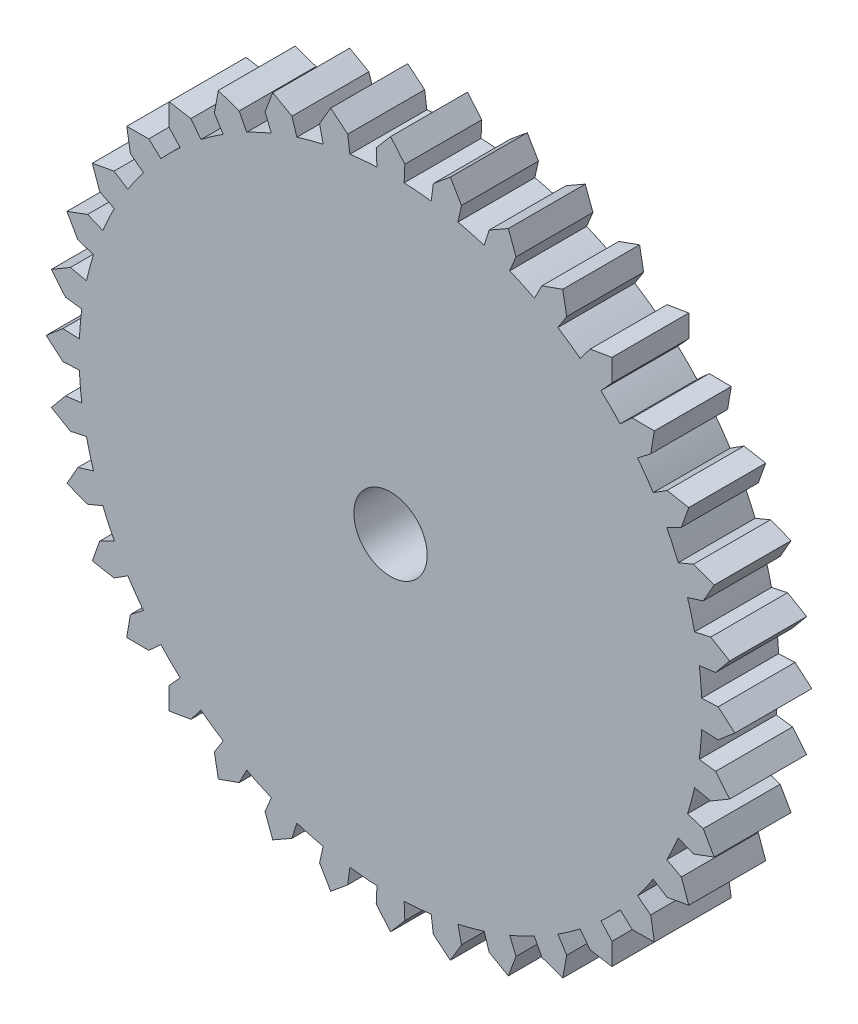
SolidWorks part; units mm, degrees
ref_plane "Front Plane" through (0, 0, 0) normal (0, 0, 1) x (1, 0, 0)
ref_plane "Top Plane" through (0, 0, 0) normal (0, 1, 0) x (1, 0, 0)
ref_plane "Right Plane" through (0, 0, 0) normal (1, 0, 0) x (0, 0, -1)
sketch "Sketch1" plane through (0, 0, 0) normal (0, 0, 1) x (1, 0, 0)
  line L0 (1.6323, 9.2572) -> (1.9371, 8.7378)
  line L1 (0, 9.4) -> (0.3904, 8.9415)
  line L2 (-0.3708, 8.4919) -> (-0.3904, 8.9415)
  line L3 (0, 9.4) -> (-0.3904, 8.9415)
  line L4 (0.3708, 8.4919) -> (0.3904, 8.9415)
  line L5 (1.1095, 8.4273) -> (1.1682, 8.8734)
  line L6 (1.6323, 9.2572) -> (1.1682, 8.8734)
  line L7 (1.8397, 8.2985) -> (1.9371, 8.7378)
  line L8 (3.215, 8.8331) -> (3.425, 8.2687)
  line L9 (2.556, 8.1066) -> (2.6913, 8.5358)
  line L10 (3.215, 8.8331) -> (2.6913, 8.5358)
  line L11 (3.2528, 7.853) -> (3.425, 8.2687)
  line L12 (4.7, 8.1406) -> (4.8088, 7.5484)
  line L13 (3.9249, 7.5396) -> (4.1327, 7.9387)
  line L14 (4.7, 8.1406) -> (4.1327, 7.9387)
  line L15 (4.567, 7.1688) -> (4.8088, 7.5484)
  line L16 (6.0422, 7.2008) -> (6.0465, 6.5986)
  line L17 (5.1745, 6.7435) -> (5.4484, 7.1005)
  line L18 (6.0422, 7.2008) -> (5.4484, 7.1005)
  line L19 (5.7425, 6.2669) -> (6.0465, 6.5986)
  line L20 (7.2008, 6.0422) -> (7.1005, 5.4484)
  line L21 (6.2669, 5.7425) -> (6.5986, 6.0465)
  line L22 (7.2008, 6.0422) -> (6.5986, 6.0465)
  line L23 (6.7435, 5.1745) -> (7.1005, 5.4484)
  line L24 (8.1406, 4.7) -> (7.9387, 4.1327)
  line L25 (7.1688, 4.567) -> (7.5484, 4.8088)
  line L26 (8.1406, 4.7) -> (7.5484, 4.8088)
  line L27 (7.5396, 3.9249) -> (7.9387, 4.1327)
  line L28 (8.8331, 3.215) -> (8.5358, 2.6913)
  line L29 (7.853, 3.2528) -> (8.2687, 3.425)
  line L30 (8.8331, 3.215) -> (8.2687, 3.425)
  line L31 (8.1066, 2.556) -> (8.5358, 2.6913)
  line L32 (9.2572, 1.6323) -> (8.8734, 1.1682)
  line L33 (8.2985, 1.8397) -> (8.7378, 1.9371)
  line L34 (9.2572, 1.6323) -> (8.7378, 1.9371)
  line L35 (8.4273, 1.1095) -> (8.8734, 1.1682)
  line L36 (9.4, 0) -> (8.9415, -0.3904)
  line L37 (8.4919, 0.3708) -> (8.9415, 0.3904)
  line L38 (9.4, 0) -> (8.9415, 0.3904)
  line L39 (8.4919, -0.3708) -> (8.9415, -0.3904)
  line L40 (9.2572, -1.6323) -> (8.7378, -1.9371)
  line L41 (8.4273, -1.1095) -> (8.8734, -1.1682)
  line L42 (9.2572, -1.6323) -> (8.8734, -1.1682)
  line L43 (8.2985, -1.8397) -> (8.7378, -1.9371)
  line L44 (8.8331, -3.215) -> (8.2687, -3.425)
  line L45 (8.1066, -2.556) -> (8.5358, -2.6913)
  line L46 (8.8331, -3.215) -> (8.5358, -2.6913)
  line L47 (7.853, -3.2528) -> (8.2687, -3.425)
  line L48 (8.1406, -4.7) -> (7.5484, -4.8088)
  line L49 (7.5396, -3.9249) -> (7.9387, -4.1327)
  line L50 (8.1406, -4.7) -> (7.9387, -4.1327)
  line L51 (7.1688, -4.567) -> (7.5484, -4.8088)
  line L52 (7.2008, -6.0422) -> (6.5986, -6.0465)
  line L53 (6.7435, -5.1745) -> (7.1005, -5.4484)
  line L54 (7.2008, -6.0422) -> (7.1005, -5.4484)
  line L55 (6.2669, -5.7425) -> (6.5986, -6.0465)
  line L56 (6.0422, -7.2008) -> (5.4484, -7.1005)
  line L57 (5.7425, -6.2669) -> (6.0465, -6.5986)
  line L58 (6.0422, -7.2008) -> (6.0465, -6.5986)
  line L59 (5.1745, -6.7435) -> (5.4484, -7.1005)
  line L60 (4.7, -8.1406) -> (4.1327, -7.9387)
  line L61 (4.567, -7.1688) -> (4.8088, -7.5484)
  line L62 (4.7, -8.1406) -> (4.8088, -7.5484)
  line L63 (3.9249, -7.5396) -> (4.1327, -7.9387)
  line L64 (3.215, -8.8331) -> (2.6913, -8.5358)
  line L65 (3.2528, -7.853) -> (3.425, -8.2687)
  line L66 (3.215, -8.8331) -> (3.425, -8.2687)
  line L67 (2.556, -8.1066) -> (2.6913, -8.5358)
  line L68 (1.6323, -9.2572) -> (1.1682, -8.8734)
  line L69 (1.8397, -8.2985) -> (1.9371, -8.7378)
  line L70 (1.6323, -9.2572) -> (1.9371, -8.7378)
  line L71 (1.1095, -8.4273) -> (1.1682, -8.8734)
  line L72 (0, -9.4) -> (-0.3904, -8.9415)
  line L73 (0.3708, -8.4919) -> (0.3904, -8.9415)
  line L74 (0, -9.4) -> (0.3904, -8.9415)
  line L75 (-0.3708, -8.4919) -> (-0.3904, -8.9415)
  line L76 (-1.6323, -9.2572) -> (-1.9371, -8.7378)
  line L77 (-1.1095, -8.4273) -> (-1.1682, -8.8734)
  line L78 (-1.6323, -9.2572) -> (-1.1682, -8.8734)
  line L79 (-1.8397, -8.2985) -> (-1.9371, -8.7378)
  line L80 (-3.215, -8.8331) -> (-3.425, -8.2687)
  line L81 (-2.556, -8.1066) -> (-2.6913, -8.5358)
  line L82 (-3.215, -8.8331) -> (-2.6913, -8.5358)
  line L83 (-3.2528, -7.853) -> (-3.425, -8.2687)
  line L84 (-4.7, -8.1406) -> (-4.8088, -7.5484)
  line L85 (-3.9249, -7.5396) -> (-4.1327, -7.9387)
  line L86 (-4.7, -8.1406) -> (-4.1327, -7.9387)
  line L87 (-4.567, -7.1688) -> (-4.8088, -7.5484)
  line L88 (-6.0422, -7.2008) -> (-6.0465, -6.5986)
  line L89 (-5.1745, -6.7435) -> (-5.4484, -7.1005)
  line L90 (-6.0422, -7.2008) -> (-5.4484, -7.1005)
  line L91 (-5.7425, -6.2669) -> (-6.0465, -6.5986)
  line L92 (-7.2008, -6.0422) -> (-7.1005, -5.4484)
  line L93 (-6.2669, -5.7425) -> (-6.5986, -6.0465)
  line L94 (-7.2008, -6.0422) -> (-6.5986, -6.0465)
  line L95 (-6.7435, -5.1745) -> (-7.1005, -5.4484)
  line L96 (-8.1406, -4.7) -> (-7.9387, -4.1327)
  line L97 (-7.1688, -4.567) -> (-7.5484, -4.8088)
  line L98 (-8.1406, -4.7) -> (-7.5484, -4.8088)
  line L99 (-7.5396, -3.9249) -> (-7.9387, -4.1327)
  line L100 (-8.8331, -3.215) -> (-8.5358, -2.6913)
  line L101 (-7.853, -3.2528) -> (-8.2687, -3.425)
  line L102 (-8.8331, -3.215) -> (-8.2687, -3.425)
  line L103 (-8.1066, -2.556) -> (-8.5358, -2.6913)
  line L104 (-9.2572, -1.6323) -> (-8.8734, -1.1682)
  line L105 (-8.2985, -1.8397) -> (-8.7378, -1.9371)
  line L106 (-9.2572, -1.6323) -> (-8.7378, -1.9371)
  line L107 (-8.4273, -1.1095) -> (-8.8734, -1.1682)
  line L108 (-9.4, 0) -> (-8.9415, 0.3904)
  line L109 (-8.4919, -0.3708) -> (-8.9415, -0.3904)
  line L110 (-9.4, 0) -> (-8.9415, -0.3904)
  line L111 (-8.4919, 0.3708) -> (-8.9415, 0.3904)
  line L112 (-9.2572, 1.6323) -> (-8.7378, 1.9371)
  line L113 (-8.4273, 1.1095) -> (-8.8734, 1.1682)
  line L114 (-9.2572, 1.6323) -> (-8.8734, 1.1682)
  line L115 (-8.2985, 1.8397) -> (-8.7378, 1.9371)
  line L116 (-8.8331, 3.215) -> (-8.2687, 3.425)
  line L117 (-8.1066, 2.556) -> (-8.5358, 2.6913)
  line L118 (-8.8331, 3.215) -> (-8.5358, 2.6913)
  line L119 (-7.853, 3.2528) -> (-8.2687, 3.425)
  line L120 (-8.1406, 4.7) -> (-7.5484, 4.8088)
  line L121 (-7.5396, 3.9249) -> (-7.9387, 4.1327)
  line L122 (-8.1406, 4.7) -> (-7.9387, 4.1327)
  line L123 (-7.1688, 4.567) -> (-7.5484, 4.8088)
  line L124 (-7.2008, 6.0422) -> (-6.5986, 6.0465)
  line L125 (-6.7435, 5.1745) -> (-7.1005, 5.4484)
  line L126 (-7.2008, 6.0422) -> (-7.1005, 5.4484)
  line L127 (-6.2669, 5.7425) -> (-6.5986, 6.0465)
  line L128 (-6.0422, 7.2008) -> (-5.4484, 7.1005)
  line L129 (-5.7425, 6.2669) -> (-6.0465, 6.5986)
  line L130 (-6.0422, 7.2008) -> (-6.0465, 6.5986)
  line L131 (-5.1745, 6.7435) -> (-5.4484, 7.1005)
  line L132 (-4.7, 8.1406) -> (-4.1327, 7.9387)
  line L133 (-4.567, 7.1688) -> (-4.8088, 7.5484)
  line L134 (-4.7, 8.1406) -> (-4.8088, 7.5484)
  line L135 (-3.9249, 7.5396) -> (-4.1327, 7.9387)
  line L136 (-3.215, 8.8331) -> (-2.6913, 8.5358)
  line L137 (-3.2528, 7.853) -> (-3.425, 8.2687)
  line L138 (-3.215, 8.8331) -> (-3.425, 8.2687)
  line L139 (-2.556, 8.1066) -> (-2.6913, 8.5358)
  line L140 (-1.6323, 9.2572) -> (-1.1682, 8.8734)
  line L141 (-1.8397, 8.2985) -> (-1.9371, 8.7378)
  line L142 (-1.6323, 9.2572) -> (-1.9371, 8.7378)
  line L143 (-1.1095, 8.4273) -> (-1.1682, 8.8734)
  arc A0 (0.3708, 8.4919) -> (0.7408, 8.4677) centre (0, 0) cw
  arc A1 (-0.3708, 8.4919) -> (-0.7408, 8.4677) centre (0, 0) ccw
  arc A2 (1.8397, 8.2985) -> (2.2, 8.2104) centre (0, 0) cw
  arc A3 (1.1095, 8.4273) -> (0.7408, 8.4677) centre (0, 0) ccw
  arc A4 (3.2528, 7.853) -> (3.5923, 7.7036) centre (0, 0) cw
  arc A5 (2.556, 8.1066) -> (2.2, 8.2104) centre (0, 0) ccw
  arc A6 (4.567, 7.1688) -> (4.8754, 6.9628) centre (0, 0) cw
  arc A7 (3.9249, 7.5396) -> (3.5923, 7.7036) centre (0, 0) ccw
  arc A8 (5.7425, 6.2669) -> (6.0104, 6.0104) centre (0, 0) cw
  arc A9 (5.1745, 6.7435) -> (4.8754, 6.9628) centre (0, 0) ccw
  arc A10 (6.7435, 5.1745) -> (6.9628, 4.8754) centre (0, 0) cw
  arc A11 (6.2669, 5.7425) -> (6.0104, 6.0104) centre (0, 0) ccw
  arc A12 (7.5396, 3.9249) -> (7.7036, 3.5923) centre (0, 0) cw
  arc A13 (7.1688, 4.567) -> (6.9628, 4.8754) centre (0, 0) ccw
  arc A14 (8.1066, 2.556) -> (8.2104, 2.2) centre (0, 0) cw
  arc A15 (7.853, 3.2528) -> (7.7036, 3.5923) centre (0, 0) ccw
  arc A16 (8.4273, 1.1095) -> (8.4677, 0.7408) centre (0, 0) cw
  arc A17 (8.2985, 1.8397) -> (8.2104, 2.2) centre (0, 0) ccw
  arc A18 (8.4919, -0.3708) -> (8.4677, -0.7408) centre (0, 0) cw
  arc A19 (8.4919, 0.3708) -> (8.4677, 0.7408) centre (0, 0) ccw
  arc A20 (8.2985, -1.8397) -> (8.2104, -2.2) centre (0, 0) cw
  arc A21 (8.4273, -1.1095) -> (8.4677, -0.7408) centre (0, 0) ccw
  arc A22 (7.853, -3.2528) -> (7.7036, -3.5923) centre (0, 0) cw
  arc A23 (8.1066, -2.556) -> (8.2104, -2.2) centre (0, 0) ccw
  arc A24 (7.1688, -4.567) -> (6.9628, -4.8754) centre (0, 0) cw
  arc A25 (7.5396, -3.9249) -> (7.7036, -3.5923) centre (0, 0) ccw
  arc A26 (6.2669, -5.7425) -> (6.0104, -6.0104) centre (0, 0) cw
  arc A27 (6.7435, -5.1745) -> (6.9628, -4.8754) centre (0, 0) ccw
  arc A28 (5.1745, -6.7435) -> (4.8754, -6.9628) centre (0, 0) cw
  arc A29 (5.7425, -6.2669) -> (6.0104, -6.0104) centre (0, 0) ccw
  arc A30 (3.9249, -7.5396) -> (3.5923, -7.7036) centre (0, 0) cw
  arc A31 (4.567, -7.1688) -> (4.8754, -6.9628) centre (0, 0) ccw
  arc A32 (2.556, -8.1066) -> (2.2, -8.2104) centre (0, 0) cw
  arc A33 (3.2528, -7.853) -> (3.5923, -7.7036) centre (0, 0) ccw
  arc A34 (1.1095, -8.4273) -> (0.7408, -8.4677) centre (0, 0) cw
  arc A35 (1.8397, -8.2985) -> (2.2, -8.2104) centre (0, 0) ccw
  arc A36 (-0.3708, -8.4919) -> (-0.7408, -8.4677) centre (0, 0) cw
  arc A37 (0.3708, -8.4919) -> (0.7408, -8.4677) centre (0, 0) ccw
  arc A38 (-1.8397, -8.2985) -> (-2.2, -8.2104) centre (0, 0) cw
  arc A39 (-1.1095, -8.4273) -> (-0.7408, -8.4677) centre (0, 0) ccw
  arc A40 (-3.2528, -7.853) -> (-3.5923, -7.7036) centre (0, 0) cw
  arc A41 (-2.556, -8.1066) -> (-2.2, -8.2104) centre (0, 0) ccw
  arc A42 (-4.567, -7.1688) -> (-4.8754, -6.9628) centre (0, 0) cw
  arc A43 (-3.9249, -7.5396) -> (-3.5923, -7.7036) centre (0, 0) ccw
  arc A44 (-5.7425, -6.2669) -> (-6.0104, -6.0104) centre (0, 0) cw
  arc A45 (-5.1745, -6.7435) -> (-4.8754, -6.9628) centre (0, 0) ccw
  arc A46 (-6.7435, -5.1745) -> (-6.9628, -4.8754) centre (0, 0) cw
  arc A47 (-6.2669, -5.7425) -> (-6.0104, -6.0104) centre (0, 0) ccw
  arc A48 (-7.5396, -3.9249) -> (-7.7036, -3.5923) centre (0, 0) cw
  arc A49 (-7.1688, -4.567) -> (-6.9628, -4.8754) centre (0, 0) ccw
  arc A50 (-8.1066, -2.556) -> (-8.2104, -2.2) centre (0, 0) cw
  arc A51 (-7.853, -3.2528) -> (-7.7036, -3.5923) centre (0, 0) ccw
  arc A52 (-8.4273, -1.1095) -> (-8.4677, -0.7408) centre (0, 0) cw
  arc A53 (-8.2985, -1.8397) -> (-8.2104, -2.2) centre (0, 0) ccw
  arc A54 (-8.4919, 0.3708) -> (-8.4677, 0.7408) centre (0, 0) cw
  arc A55 (-8.4919, -0.3708) -> (-8.4677, -0.7408) centre (0, 0) ccw
  arc A56 (-8.2985, 1.8397) -> (-8.2104, 2.2) centre (0, 0) cw
  arc A57 (-8.4273, 1.1095) -> (-8.4677, 0.7408) centre (0, 0) ccw
  arc A58 (-7.853, 3.2528) -> (-7.7036, 3.5923) centre (0, 0) cw
  arc A59 (-8.1066, 2.556) -> (-8.2104, 2.2) centre (0, 0) ccw
  arc A60 (-7.1688, 4.567) -> (-6.9628, 4.8754) centre (0, 0) cw
  arc A61 (-7.5396, 3.9249) -> (-7.7036, 3.5923) centre (0, 0) ccw
  arc A62 (-6.2669, 5.7425) -> (-6.0104, 6.0104) centre (0, 0) cw
  arc A63 (-6.7435, 5.1745) -> (-6.9628, 4.8754) centre (0, 0) ccw
  arc A64 (-5.1745, 6.7435) -> (-4.8754, 6.9628) centre (0, 0) cw
  arc A65 (-5.7425, 6.2669) -> (-6.0104, 6.0104) centre (0, 0) ccw
  arc A66 (-3.9249, 7.5396) -> (-3.5923, 7.7036) centre (0, 0) cw
  arc A67 (-4.567, 7.1688) -> (-4.8754, 6.9628) centre (0, 0) ccw
  arc A68 (-2.556, 8.1066) -> (-2.2, 8.2104) centre (0, 0) cw
  arc A69 (-3.2528, 7.853) -> (-3.5923, 7.7036) centre (0, 0) ccw
  arc A70 (-1.1095, 8.4273) -> (-0.7408, 8.4677) centre (0, 0) cw
  arc A71 (-1.8397, 8.2985) -> (-2.2, 8.2104) centre (0, 0) ccw
  circle A72 centre (0, 0) radius 1
  point P256 (0, 0)
  dimension "D1" = 36
  dimension "D2" = 17
  dimension "D3" = 2
extrude "Boss-Extrude1" add sketch "Sketch1" along normal blind 2.1
sketch "Sketch2" plane through (0, 0, 0) normal (0, 0, 1) x (1, 0, 0)
  line L0 (1.85, 3.2043) -> (1.8872, 2.4594)
  line L1 (0, 3.7) -> (0.4046, 3.0735)
  line L2 (-0.3263, 2.4786) -> (-0.4046, 3.0735)
  line L3 (0, 3.7) -> (-0.4046, 3.0735)
  line L4 (0.3263, 2.4786) -> (0.4046, 3.0735)
  line L5 (0.9567, 2.3097) -> (1.1863, 2.864)
  line L6 (1.85, 3.2043) -> (1.1863, 2.864)
  line L7 (1.5219, 1.9834) -> (1.8872, 2.4594)
  line L8 (3.2043, 1.85) -> (2.864, 1.1863)
  line L9 (1.9834, 1.5219) -> (2.4594, 1.8872)
  line L10 (3.2043, 1.85) -> (2.4594, 1.8872)
  line L11 (2.3097, 0.9567) -> (2.864, 1.1863)
  line L12 (3.7, 0) -> (3.0735, -0.4046)
  line L13 (2.4786, 0.3263) -> (3.0735, 0.4046)
  line L14 (3.7, 0) -> (3.0735, 0.4046)
  line L15 (2.4786, -0.3263) -> (3.0735, -0.4046)
  line L16 (3.2043, -1.85) -> (2.4594, -1.8872)
  line L17 (2.3097, -0.9567) -> (2.864, -1.1863)
  line L18 (3.2043, -1.85) -> (2.864, -1.1863)
  line L19 (1.9834, -1.5219) -> (2.4594, -1.8872)
  line L20 (1.85, -3.2043) -> (1.1863, -2.864)
  line L21 (1.5219, -1.9834) -> (1.8872, -2.4594)
  line L22 (1.85, -3.2043) -> (1.8872, -2.4594)
  line L23 (0.9567, -2.3097) -> (1.1863, -2.864)
  line L24 (0, -3.7) -> (-0.4046, -3.0735)
  line L25 (0.3263, -2.4786) -> (0.4046, -3.0735)
  line L26 (0, -3.7) -> (0.4046, -3.0735)
  line L27 (-0.3263, -2.4786) -> (-0.4046, -3.0735)
  line L28 (-1.85, -3.2043) -> (-1.8872, -2.4594)
  line L29 (-0.9567, -2.3097) -> (-1.1863, -2.864)
  line L30 (-1.85, -3.2043) -> (-1.1863, -2.864)
  line L31 (-1.5219, -1.9834) -> (-1.8872, -2.4594)
  line L32 (-3.2043, -1.85) -> (-2.864, -1.1863)
  line L33 (-1.9834, -1.5219) -> (-2.4594, -1.8872)
  line L34 (-3.2043, -1.85) -> (-2.4594, -1.8872)
  line L35 (-2.3097, -0.9567) -> (-2.864, -1.1863)
  line L36 (-3.7, 0) -> (-3.0735, 0.4046)
  line L37 (-2.4786, -0.3263) -> (-3.0735, -0.4046)
  line L38 (-3.7, 0) -> (-3.0735, -0.4046)
  line L39 (-2.4786, 0.3263) -> (-3.0735, 0.4046)
  line L40 (-3.2043, 1.85) -> (-2.4594, 1.8872)
  line L41 (-2.3097, 0.9567) -> (-2.864, 1.1863)
  line L42 (-3.2043, 1.85) -> (-2.864, 1.1863)
  line L43 (-1.9834, 1.5219) -> (-2.4594, 1.8872)
  line L44 (-1.85, 3.2043) -> (-1.1863, 2.864)
  line L45 (-1.5219, 1.9834) -> (-1.8872, 2.4594)
  line L46 (-1.85, 3.2043) -> (-1.8872, 2.4594)
  line L47 (-0.9567, 2.3097) -> (-1.1863, 2.864)
  arc A0 (0.3263, 2.4786) -> (0.647, 2.4148) centre (0, 0) cw
  arc A1 (-0.3263, 2.4786) -> (-0.647, 2.4148) centre (0, 0) ccw
  arc A2 (1.5219, 1.9834) -> (1.7678, 1.7678) centre (0, 0) cw
  arc A3 (0.9567, 2.3097) -> (0.647, 2.4148) centre (0, 0) ccw
  arc A4 (2.3097, 0.9567) -> (2.4148, 0.647) centre (0, 0) cw
  arc A5 (1.9834, 1.5219) -> (1.7678, 1.7678) centre (0, 0) ccw
  arc A6 (2.4786, -0.3263) -> (2.4148, -0.647) centre (0, 0) cw
  arc A7 (2.4786, 0.3263) -> (2.4148, 0.647) centre (0, 0) ccw
  arc A8 (1.9834, -1.5219) -> (1.7678, -1.7678) centre (0, 0) cw
  arc A9 (2.3097, -0.9567) -> (2.4148, -0.647) centre (0, 0) ccw
  arc A10 (0.9567, -2.3097) -> (0.647, -2.4148) centre (0, 0) cw
  arc A11 (1.5219, -1.9834) -> (1.7678, -1.7678) centre (0, 0) ccw
  arc A12 (-0.3263, -2.4786) -> (-0.647, -2.4148) centre (0, 0) cw
  arc A13 (0.3263, -2.4786) -> (0.647, -2.4148) centre (0, 0) ccw
  arc A14 (-1.5219, -1.9834) -> (-1.7678, -1.7678) centre (0, 0) cw
  arc A15 (-0.9567, -2.3097) -> (-0.647, -2.4148) centre (0, 0) ccw
  arc A16 (-2.3097, -0.9567) -> (-2.4148, -0.647) centre (0, 0) cw
  arc A17 (-1.9834, -1.5219) -> (-1.7678, -1.7678) centre (0, 0) ccw
  arc A18 (-2.4786, 0.3263) -> (-2.4148, 0.647) centre (0, 0) cw
  arc A19 (-2.4786, -0.3263) -> (-2.4148, -0.647) centre (0, 0) ccw
  arc A20 (-1.9834, 1.5219) -> (-1.7678, 1.7678) centre (0, 0) cw
  arc A21 (-2.3097, 0.9567) -> (-2.4148, 0.647) centre (0, 0) ccw
  arc A22 (-0.9567, 2.3097) -> (-0.647, 2.4148) centre (0, 0) cw
  arc A23 (-1.5219, 1.9834) -> (-1.7678, 1.7678) centre (0, 0) ccw
  circle A24 centre (0, 0) radius 1 construction
  circle A25 centre (0, 0) radius 1
  point P88 (0, 0)
  dimension "D1" = 12
  dimension "D2" = 5
extrude "Boss-Extrude2" add sketch "Sketch2" against normal blind 3.5
